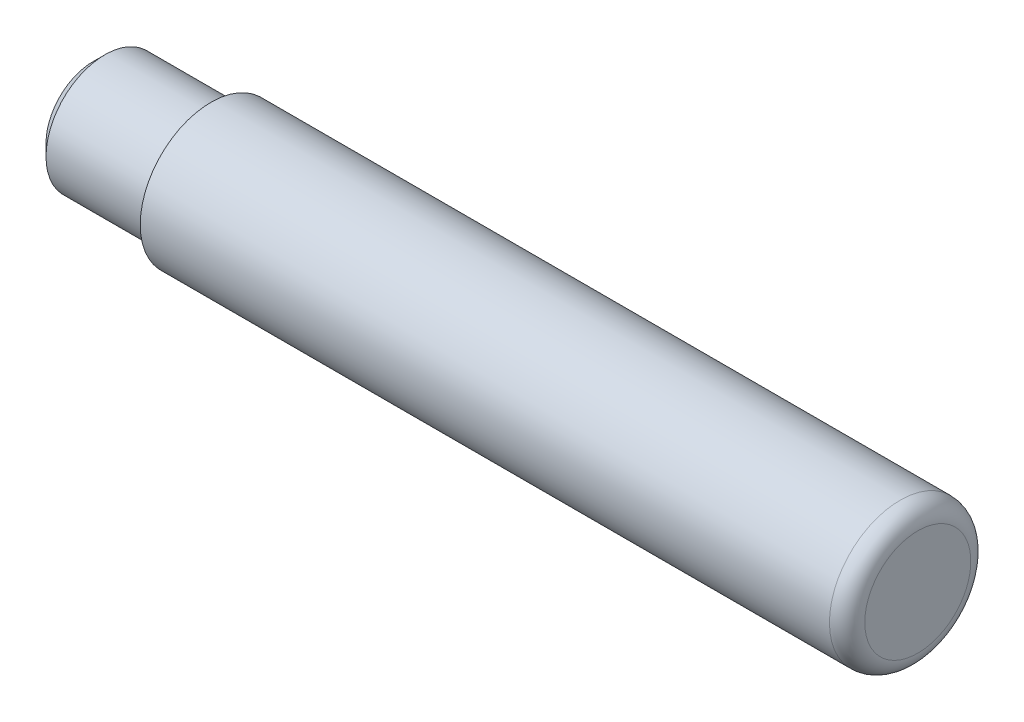
SolidWorks part; units mm, degrees
material "Stub"
ref_plane "Face" through (0, 0, 0) normal (0, 0, 1) x (1, 0, 0)
ref_plane "Dessus" through (0, 0, 0) normal (0, 1, 0) x (1, 0, 0)
ref_plane "Droite" through (0, 0, 0) normal (1, 0, 0) x (0, 0, -1)
sketch "Esquisse1" plane through (0, 0, 0) normal (0, 0, 1) x (1, 0, 0)
  line L0 (0, 0) -> (0, 4.5)
  line L1 (-1.5, 6) -> (-60, 6)
  line L2 (-60, 6) -> (-60, 5)
  line L3 (-60, 5) -> (-69, 5)
  line L4 (-70, 4) -> (-70, 0)
  line L5 (-70, 0) -> (0, 0)
  line L6 (0, 0) -> (-0.0066, -0.0902)
  line L7 (-69, 5) -> (-70, 4)
  arc A0 (0, 4.5) -> (-1.5, 6) centre (-1.5, 4.5) ccw
  point P6 (-70, 5)
  point P10 (0, 6)
  dimension "D5" = 1.5
  dimension "D1" = 60
  dimension "D2" = 6
  dimension "D3" = 5
  dimension "D4" = 10
revolve "Révolution1" add sketch "Esquisse1" angle 360 about L5
cosmetic thread "Représentation de filetage1" parameters "D2"=6.619
